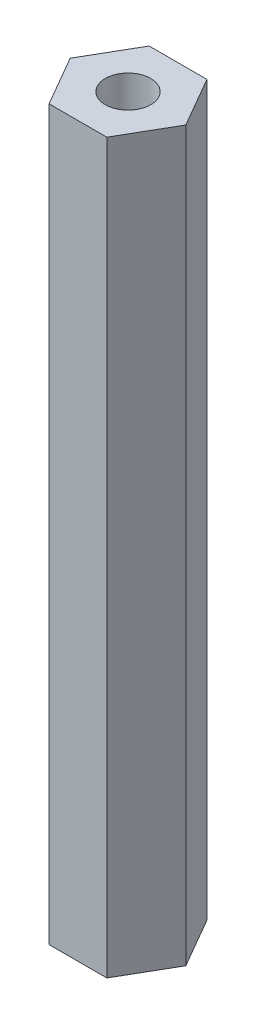
SolidWorks part; units mm, degrees
material "Stainless Steel (ferritic)"
ref_plane "Front Plane" through (0, 0, 0) normal (0, 0, 1) x (1, 0, 0)
ref_plane "Top Plane" through (0, 0, 0) normal (0, 1, 0) x (1, 0, 0)
ref_plane "Right Plane" through (0, 0, 0) normal (1, 0, 0) x (0, 0, -1)
sketch "Sketch1" plane through (0, 0, 0) normal (0, 1, 0) x (1, 0, 0)
  line L1 (3.1754, 0) -> (1.5877, 2.75)
  line L2 (1.5877, 2.75) -> (-1.5877, 2.75)
  line L3 (-1.5877, 2.75) -> (-3.1754, 0)
  line L4 (-3.1754, 0) -> (-1.5877, -2.75)
  line L5 (-1.5877, -2.75) -> (1.5877, -2.75)
  line L6 (1.5877, -2.75) -> (3.1754, 0)
  circle A0 centre (0, 0) radius 2.75 construction
  dimension "D1" = 5.5
extrude "Boss-Extrude1" add sketch "Sketch1" along normal mid plane 40
hole_wizard "M3 Tapped Hole1" positions "Sketch3" profile "Sketch2" tap size "M3" standard "DIN" end condition through all
sketch "Sketch3" plane through (0, 20, 0) normal (0, 1, 0) x (1, 0, 0)
  point P0 (0, 0)
cosmetic thread "Hole Thread1" parameters "D2"=3
sketch "Sketch2" plane through (0, 20, 0) normal (1, 0, 0) x (0, 0, 1)
  line L0 (0, 0) -> (0, 40)
  line L1 (0, 40) -> (1.25, 40)
  line L2 (1.25, 40) -> (1.25, 0)
  line L5 (1.25, 0) -> (0, 0)
  line L11 (0, -6.35) -> (0, 107.95) construction
  dimension "Thru Tap Drill Dia." = 2.5
  dimension "Thru Tap Drill Depth" = 40
